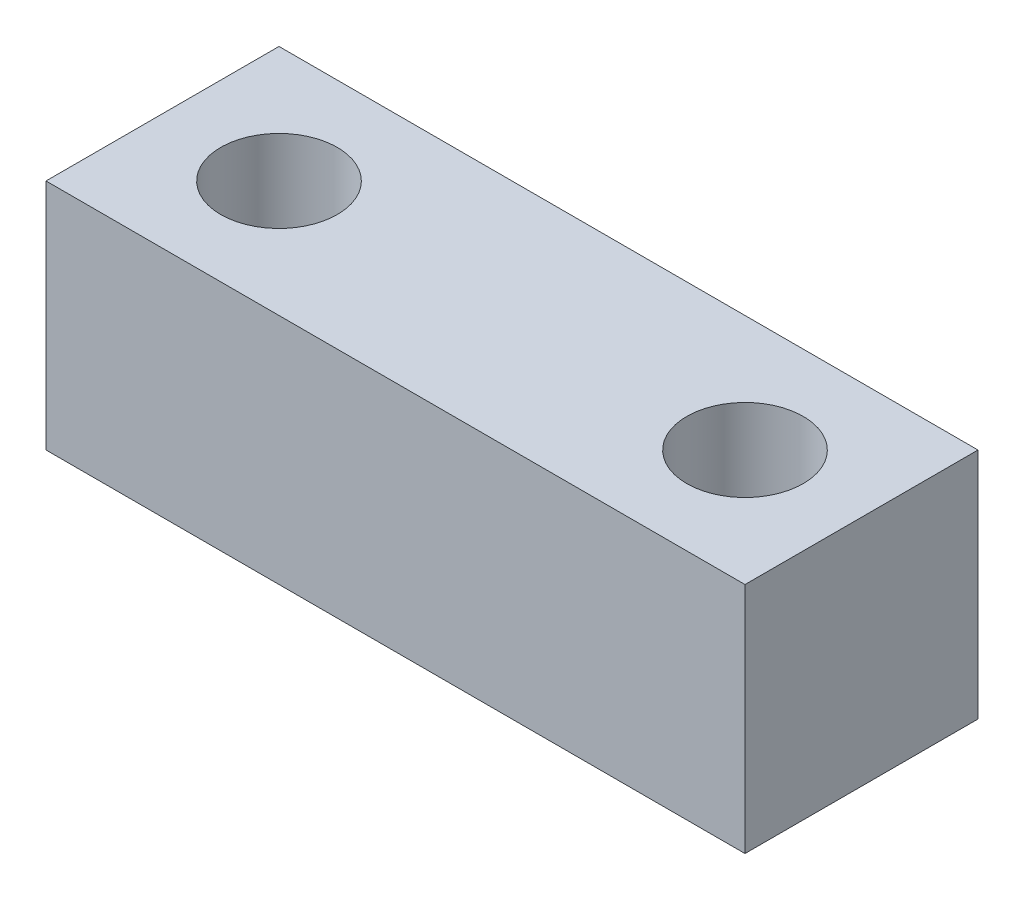
SolidWorks part; units mm, degrees
ref_plane "Front Plane" through (0, 0, 0) normal (0, 0, 1) x (1, 0, 0)
ref_plane "Top Plane" through (0, 0, 0) normal (0, 1, 0) x (1, 0, 0)
ref_plane "Right Plane" through (0, 0, 0) normal (1, 0, 0) x (0, 0, -1)
sketch "Sketch1" plane through (0, 0, 0) normal (0, 1, 0) x (1, 0, 0)
  line L1 (0, 0) -> (-76.2, 0)
  line L2 (0, 0) -> (0, 25.4)
  line L3 (0, 25.4) -> (-76.2, 25.4)
  line L4 (-76.2, 0) -> (-76.2, 25.4)
  circle A0 centre (-63.5, 12.7) radius 6.35
  circle A1 centre (-12.7, 12.7) radius 6.35
  point P9 (0, 12.7)
  dimension "D3" = 12.7
  dimension "D4" = 12.7
  dimension "D1" = 76.2
  dimension "D2" = 25.4
  dimension "D5" = 12.7
  dimension "D6" = 12.7
  dimension "D7" = 12.7
  dimension "D8" = 12.7
extrude "Boss-Extrude1" add sketch "Sketch1" along normal blind 25.4
